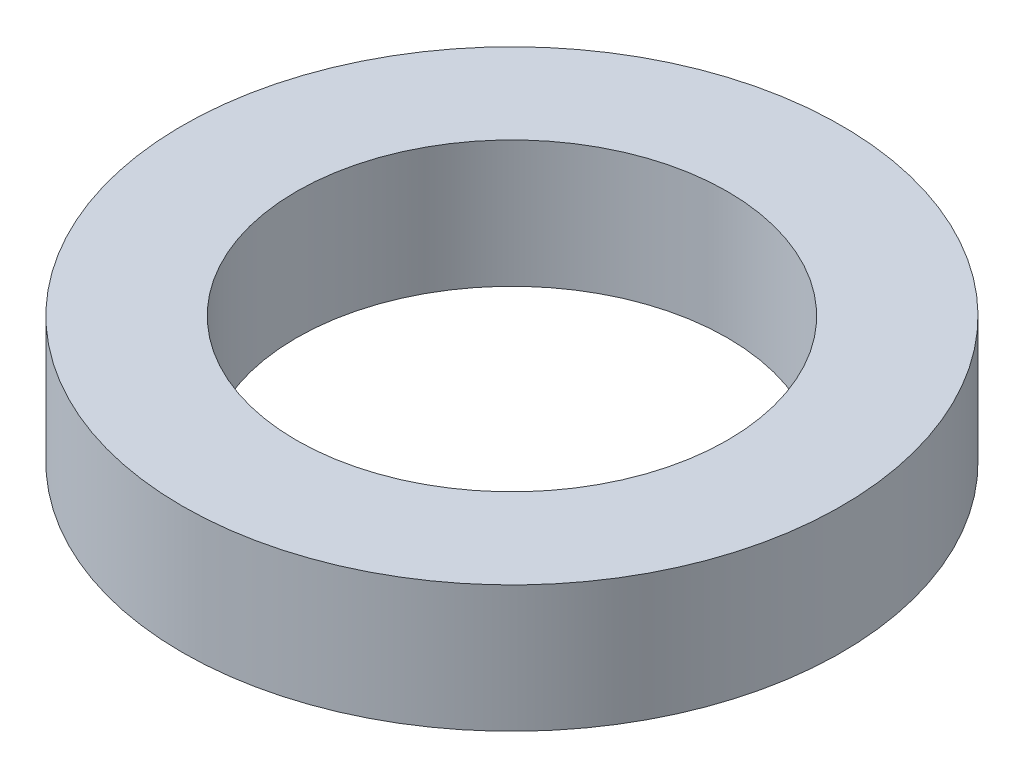
SolidWorks part; units mm, degrees
material "Malleable Cast Iron"
ref_plane "Front Plane" through (0, 0, 0) normal (0, 0, 1) x (1, 0, 0)
ref_plane "Top Plane" through (0, 0, 0) normal (0, 1, 0) x (1, 0, 0)
ref_plane "Right Plane" through (0, 0, 0) normal (1, 0, 0) x (0, 0, -1)
sketch "Sketch1" plane through (0, 0, 0) normal (0, 1, 0) x (1, 0, 0)
  circle A0 centre (0, 0) radius 8.5
  circle A1 centre (0, 0) radius 13
extrude "Boss-Extrude1" add sketch "Sketch1" along normal blind 5
